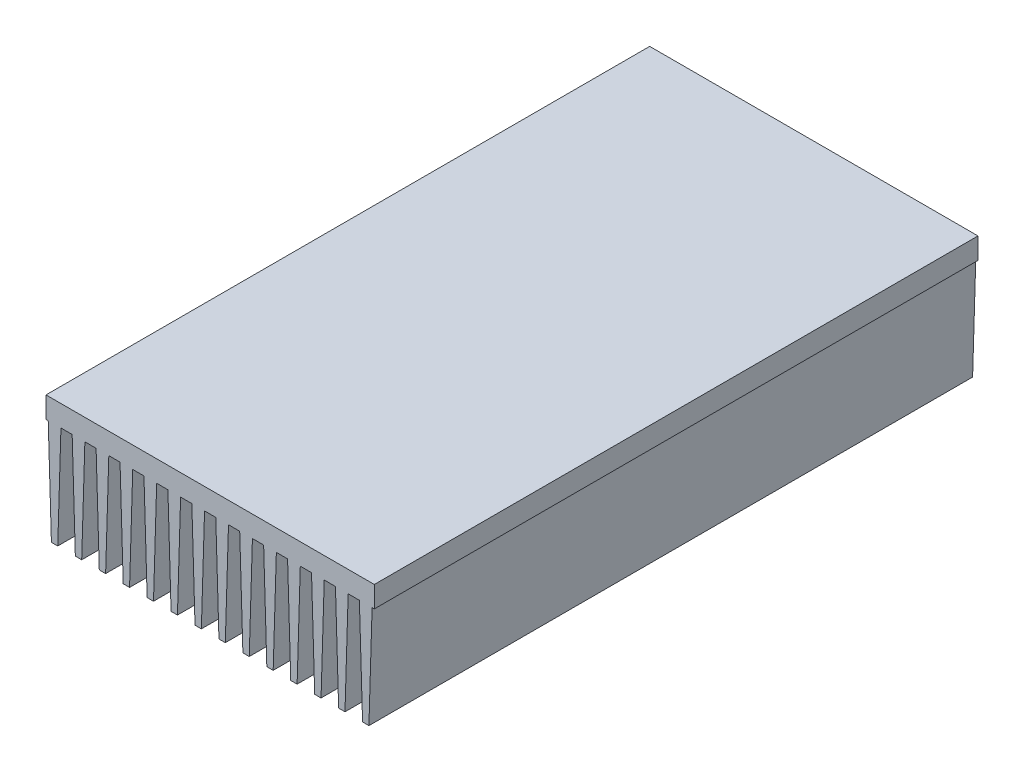
SolidWorks part; units mm, degrees
ref_plane "Plano frontal" through (0, 0, 0) normal (0, 0, 1) x (1, 0, 0)
ref_plane "Plano superior" through (0, 0, 0) normal (0, 1, 0) x (1, 0, 0)
ref_plane "Plano direito" through (0, 0, 0) normal (1, 0, 0) x (0, 0, -1)
sketch "Esboço1" plane through (0, 0, 0) normal (0, 0, 1) x (1, 0, 0)
  line L0 (0, 59) -> (155, 59)
  line L3 (0, 0) -> (131.9536, 0) construction
  line L4 (0, 49) -> (0, 59)
  line L46 (29.65, 49) -> (34.95, 49)
  line L47 (34.95, 49) -> (40.95, 49) construction
  line L48 (40.95, 49) -> (46.25, 49)
  line L49 (46.25, 49) -> (52.25, 49) construction
  line L50 (52.25, 49) -> (57.55, 49)
  line L51 (57.55, 49) -> (63.55, 49) construction
  line L52 (63.55, 49) -> (68.85, 49)
  line L53 (68.85, 49) -> (74.85, 49) construction
  line L54 (74.85, 49) -> (80.15, 49)
  line L57 (0, 0) -> (0, 59) construction
  line L59 (0, 49) -> (1.05, 49)
  line L61 (1.05, 49) -> (7.05, 49) construction
  line L63 (7.05, 49) -> (12.35, 49)
  line L65 (12.35, 49) -> (18.35, 49) construction
  line L66 (29.65, 49) -> (28.15, 0)
  line L68 (34.95, 49) -> (36.45, 0)
  line L69 (36.45, 0) -> (39.45, 0)
  line L70 (39.45, 0) -> (40.95, 49)
  line L71 (46.25, 49) -> (47.75, 0)
  line L72 (47.75, 0) -> (50.75, 0)
  line L73 (50.75, 0) -> (52.25, 49)
  line L74 (57.55, 49) -> (59.05, 0)
  line L75 (59.05, 0) -> (62.05, 0)
  line L76 (62.05, 0) -> (63.55, 49)
  line L77 (68.85, 49) -> (70.35, 0)
  line L78 (70.35, 0) -> (73.35, 0)
  line L79 (73.35, 0) -> (74.85, 49)
  line L97 (77.5, 49) -> (77.5, 59) construction
  line L98 (37.95, 0) -> (37.95, 49) construction
  line L99 (18.35, 49) -> (23.65, 49)
  line L100 (23.65, 49) -> (29.65, 49) construction
  line L101 (131.35, 49) -> (125.35, 49) construction
  line L102 (117.05, 0) -> (117.05, 49) construction
  line L103 (142.65, 49) -> (136.65, 49) construction
  line L104 (153.95, 49) -> (147.95, 49) construction
  line L105 (1.05, 49) -> (2.55, 0)
  line L106 (2.55, 0) -> (5.55, 0)
  line L107 (5.55, 0) -> (7.05, 49)
  line L108 (12.35, 49) -> (13.85, 0)
  line L109 (13.85, 0) -> (16.85, 0)
  line L110 (16.85, 0) -> (18.35, 49)
  line L111 (23.65, 49) -> (25.15, 0)
  line L112 (25.15, 0) -> (28.15, 0)
  line L113 (86.15, 49) -> (80.15, 49) construction
  line L114 (97.45, 49) -> (91.45, 49) construction
  line L115 (108.75, 49) -> (102.75, 49) construction
  line L116 (120.05, 49) -> (114.05, 49) construction
  line L117 (129.85, 0) -> (126.85, 0)
  line L118 (131.35, 49) -> (129.85, 0)
  line L119 (138.15, 0) -> (136.65, 49)
  line L120 (141.15, 0) -> (138.15, 0)
  line L121 (142.65, 49) -> (141.15, 0)
  line L122 (149.45, 0) -> (147.95, 49)
  line L123 (152.45, 0) -> (149.45, 0)
  line L124 (153.95, 49) -> (152.45, 0)
  line L125 (136.65, 49) -> (131.35, 49)
  line L126 (81.65, 0) -> (80.15, 49)
  line L127 (84.65, 0) -> (81.65, 0)
  line L128 (86.15, 49) -> (84.65, 0)
  line L129 (92.95, 0) -> (91.45, 49)
  line L130 (95.95, 0) -> (92.95, 0)
  line L131 (97.45, 49) -> (95.95, 0)
  line L132 (104.25, 0) -> (102.75, 49)
  line L133 (107.25, 0) -> (104.25, 0)
  line L134 (108.75, 49) -> (107.25, 0)
  line L135 (115.55, 0) -> (114.05, 49)
  line L136 (118.55, 0) -> (115.55, 0)
  line L137 (120.05, 49) -> (118.55, 0)
  line L138 (125.35, 49) -> (126.85, 0)
  line L139 (147.95, 49) -> (142.65, 49)
  line L140 (155, 49) -> (153.95, 49)
  line L141 (91.45, 49) -> (86.15, 49)
  line L142 (102.75, 49) -> (97.45, 49)
  line L143 (114.05, 49) -> (108.75, 49)
  line L144 (125.35, 49) -> (120.05, 49)
  line L145 (155, 49) -> (155, 59)
  point P0 (6.6703, 49)
  point P2 (77.5, 49)
  dimension "D1" = 155
  dimension "D2" = 59
  dimension "D3" = 5.3
  dimension "D4" = 10
  dimension "D5" = 11.3
  dimension "D6" = 3
extrude "Ressalto-extrusão1" add sketch "Esboço1" along normal blind 285
